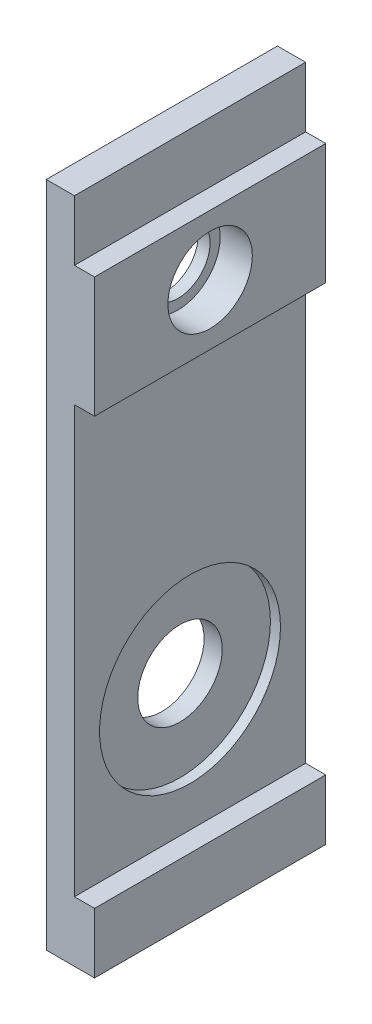
SolidWorks part; units mm, degrees
ref_plane "Alzado" through (0, 0, 0) normal (0, 0, 1) x (1, 0, 0)
ref_plane "Planta" through (0, 0, 0) normal (0, 1, 0) x (1, 0, 0)
ref_plane "Vista lateral" through (0, 0, 0) normal (1, 0, 0) x (0, 0, -1)
sketch "Croquis1" plane through (0, 0, 0) normal (0, 0, 1) x (1, 0, 0)
  line L0 (-89.2534, -13.3365) -> (-89.2534, 19.8635)
  line L1 (-89.2534, 19.8635) -> (-87.8534, 19.8635)
  line L2 (-89.2534, -13.3365) -> (-86.8534, -13.3365)
  line L3 (-86.8534, -13.3365) -> (-86.8534, -10.3365)
  line L4 (-86.8534, -10.3365) -> (-87.8534, -10.3365)
  line L5 (-87.8534, 19.8635) -> (-87.8534, 13.8635) construction
  line L6 (-87.8534, 13.8635) -> (-87.8534, 10.8635) construction
  line L7 (-87.8534, 10.8635) -> (-86.8534, 10.8635)
  line L8 (-86.8534, 10.8635) -> (-86.8534, 16.8635)
  line L9 (-86.8534, 16.8635) -> (-87.8534, 16.8635)
  line L10 (-87.8534, 16.8635) -> (-87.8534, 19.8635)
  line L11 (-87.8534, 10.8635) -> (-87.8534, -10.3365)
  dimension "D1" = 33.2
  dimension "D2" = 1.4
  dimension "D3" = 2.4
  dimension "D4" = 3
  dimension "D5" = 6
extrude "Saliente-Extruir1" add sketch "Croquis1" along normal blind 11.5
sketch "Croquis2" plane through (-86.8534, 0, 0) normal (1, 0, 0) x (0, 0, -1)
  line L0 (-11.5, 10.8635) -> (0, 16.8635) construction
  line L1 (-5.75, -13.3365) -> (-5.75, -3.8365) construction
  line L2 (-11.5, -13.3365) -> (0, -13.3365) construction
  circle A0 centre (-5.75, 13.8635) radius 2.1
  circle A1 centre (-5.75, -3.8365) radius 2.1
  dimension "D1" = 9.5
  dimension "D2" = 4.2
  dimension "D3" = 4.2
extrude "Cortar-Extruir1" cut sketch "Croquis2" against normal up to vertex
sketch "Croquis3" plane through (-87.8534, 0, 0) normal (1, 0, 0) x (0, 0, -1)
  circle A0 centre (-5.75, -3.8365) radius 4.5
  dimension "D1" = 9
extrude "Cortar-Extruir2" cut sketch "Croquis3" against normal blind 0.5
sketch "Croquis4" plane through (-89.2534, 0, 0) normal (-1, 0, 0) x (0, 0, 1)
  circle A0 centre (5.75, 13.8635) radius 3
  dimension "D1" = 6
extrude "Cortar-Extruir3" cut sketch "Croquis4" against normal blind 0.2
sketch "Croquis5" plane through (-89.0534, 0, 0) normal (-1, 0, 0) x (0, 0, 1)
  circle A0 centre (5.75, 13.8635) radius 2.1
  circle A1 centre (5.75, 13.8635) radius 1.6
  dimension "D1" = 0.5
extrude "Saliente-Extruir2" add sketch "Croquis5" against normal blind 0.6
